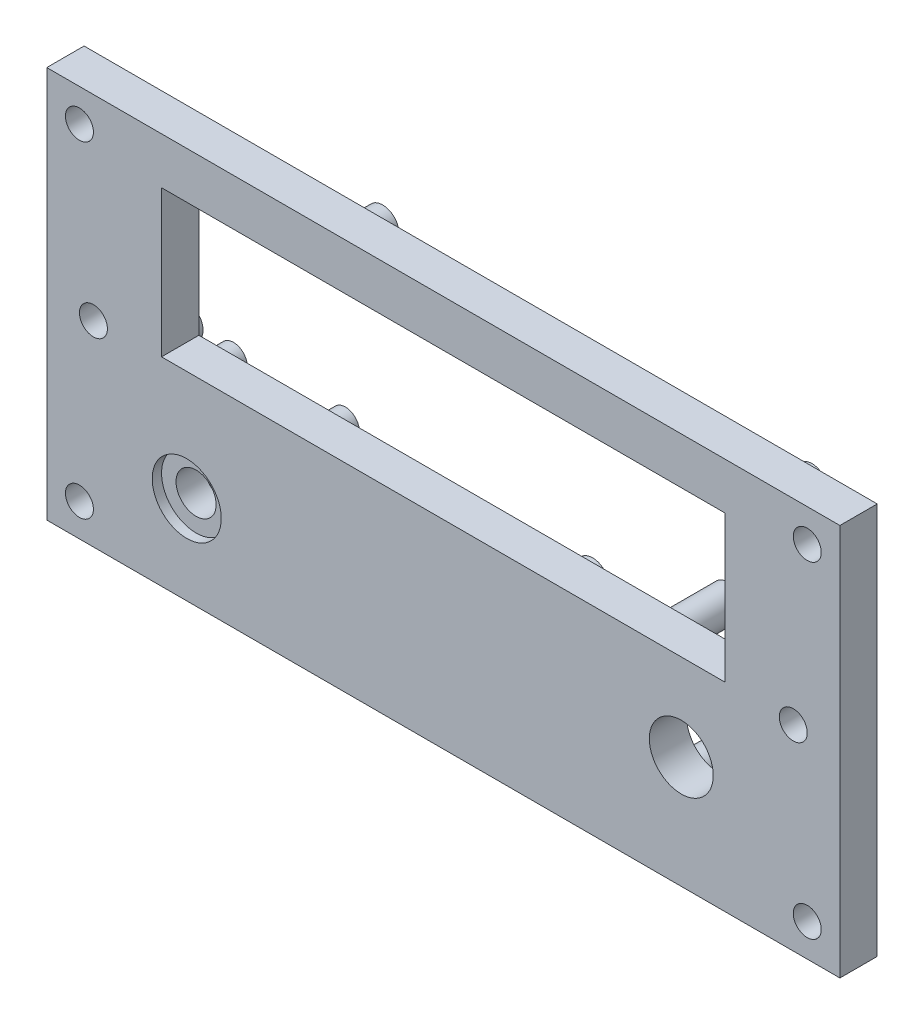
SolidWorks part; units mm, degrees
ref_plane "Front Plane" through (0, 0, 0) normal (0, 0, 1) x (1, 0, 0)
ref_plane "Top Plane" through (0, 0, 0) normal (0, 1, 0) x (1, 0, 0)
ref_plane "Right Plane" through (0, 0, 0) normal (1, 0, 0) x (0, 0, -1)
sketch "Sketch1" plane through (0, 0, 0) normal (0, 0, 1) x (1, 0, 0)
  line L1 (-42.5, 21) -> (42.5, 21)
  line L2 (-42.5, 21) -> (-42.5, -21)
  line L3 (-42.5, -21) -> (42.5, -21)
  line L4 (42.5, 21) -> (42.5, -21)
  dimension "D1" = 42
  dimension "D2" = 85
  dimension "D3" = 42.5
  dimension "D4" = 21
extrude "Bottom Plate" add sketch "Sketch1" along normal blind 4
sketch "Sketch2" plane through (0, 0, 4) normal (0, 0, 1) x (1, 0, 0)
  line L0 (-42.5, 21) -> (-42.5, -21) construction
  line L1 (42.5, 21) -> (-42.5, 21) construction
  line L2 (-52.893, 0) -> (50.3608, 0) construction
  line L3 (0, 34.5809) -> (0, -29.7625) construction
  circle A0 centre (-39, 17.5) radius 1.5
  circle A1 centre (-39, -17.5) radius 1.5
  circle A2 centre (39, -17.5) radius 1.5
  circle A3 centre (39, 17.5) radius 1.5
  dimension "D1" = 3
  dimension "D2" = 3.5
  dimension "D3" = 3.5
extrude "Bottom Plate Screw Holes" cut sketch "Sketch2" against normal through all both and the other way through all
sketch "Sketch15" plane through (0, 0, 4) normal (0, 0, 1) x (1, 0, 0)
  line L0 (0, 37.6052) -> (0, -29.8282) construction
  line L1 (-42.5, 21) -> (-42.5, -21) construction
  line L2 (-42.5, -21) -> (42.5, -21) construction
  circle A0 centre (-37.5, 0) radius 1.5
  circle A1 centre (37.5, 0) radius 1.5
  dimension "D1" = 3
  dimension "D2" = 5
  dimension "D3" = 21
  dimension "D4" = 0
extrude "Top Plate Screws Holes" cut sketch "Sketch15" against normal blind 2.5 and the other way through all
sketch "Sketch5" plane through (0, 0, 4) normal (0, 0, 1) x (1, 0, 0)
  line L1 (-30.2, 16) -> (30.2, 16)
  line L2 (-30.2, 16) -> (-30.2, 0.3)
  line L3 (-30.2, 0.3) -> (30.2, 0.3)
  line L4 (30.2, 16) -> (30.2, 0.3)
  line L5 (42.5, 21) -> (-42.5, 21) construction
  line L6 (-42.5, 21) -> (-42.5, -21) construction
  dimension "D1" = 60.4
  dimension "D2" = 15.7
  dimension "D3" = 12.3
  dimension "D4" = 5
extrude "LED" cut sketch "Sketch5" against normal through all both and the other way through all
sketch "Sketch16" plane through (0, 0, 0) normal (0, 0, -1) x (-1, 0, 0)
  line L0 (42.5, 21) -> (42.5, -21) construction
  line L1 (-42.5, 21) -> (42.5, 21) construction
  line L2 (-42.5, -21) -> (-42.5, 21) construction
  line L3 (42.5, -21) -> (-42.5, -21) construction
  circle A0 centre (-33.5, 17.5) radius 1.75
  circle A1 centre (-10, -3) radius 1.75
  circle A2 centre (33.5, -1) radius 1.75
  circle A3 centre (12.5, 18.5) radius 1.75
  circle A4 centre (13.75, -16.5) radius 1.75
  dimension "D1" = 3.5
  dimension "D2" = 3.5
  dimension "D3" = 3.5
  dimension "D4" = 3.5
  dimension "D13" = 3.5
  dimension "D5" = 9
  dimension "D6" = 22
  dimension "D7" = 30
  dimension "D8" = 2.5
  dimension "D9" = 9
  dimension "D10" = 3.5
  dimension "D11" = 32.5
  dimension "D12" = 18
  dimension "D14" = 4.5
  dimension "D15" = 28.75
extrude "LED Board Support" add sketch "Sketch16" along normal blind 2
sketch "Sketch17" plane through (0, 0, -2) normal (0, 0, -1) x (-1, 0, 0)
  circle A0 centre (-33.5, 17.5) radius 1
  circle A1 centre (-10, -3) radius 1
  circle A2 centre (12.5, 18.5) radius 1
  circle A3 centre (33.5, -1) radius 1
  circle A4 centre (13.75, -16.5) radius 1
  dimension "D1" = 2
  dimension "D2" = 2
  dimension "D3" = 2
  dimension "D4" = 2
  dimension "D5" = 2
extrude "Led Board Screws Holes" cut sketch "Sketch17" against normal blind 5
sketch "Sketch6" plane through (0, 0, 4) normal (0, 0, 1) x (1, 0, 0)
  line L0 (-42.5, 21) -> (-42.5, -21) construction
  line L1 (-42.5, -21) -> (42.5, -21) construction
  circle A0 centre (-27.5, -11.5) radius 2.15
  dimension "D1" = 4.3
  dimension "D2" = 15
  dimension "D3" = 9.5
extrude "TestButton Cut" cut sketch "Sketch6" against normal through all both
sketch "Sketch10" plane through (0, 0, 4) normal (0, 0, 1) x (1, 0, 0)
  circle A0 centre (-27.5, -11.5) radius 3.7
  dimension "D1" = 7.4
extrude "TestButton Big Cut" cut sketch "Sketch10" against normal blind 1
sketch "Sketch13" plane through (0, 0, 0) normal (0, 0, -1) x (-1, 0, 0)
  line L0 (42.5, 21) -> (42.5, -21) construction
  line L1 (42.5, -21) -> (-42.5, -21) construction
  line L2 (19.2797, -11.5) -> (38.8917, -11.5) construction
  circle A0 centre (21.5, -7) radius 1.5
  circle A1 centre (33.5, -7) radius 1.5
  circle A2 centre (33.5, -16) radius 1.5
  circle A3 centre (21.5, -16) radius 1.5
  dimension "D1" = 3
  dimension "D2" = 3
  dimension "D3" = 9
  dimension "D4" = 12
  dimension "D5" = 14
  dimension "D6" = 0
  dimension "D7" = 9.5
extrude "Test Board Support" add sketch "Sketch13" along normal blind 7
sketch "Sketch14" plane through (0, 0, -7) normal (0, 0, -1) x (-1, 0, 0)
  circle A0 centre (21.5, -16) radius 1
  circle A1 centre (21.5, -7) radius 1
  circle A2 centre (33.5, -7) radius 1
  circle A3 centre (33.5, -16) radius 1
  dimension "D1" = 2
  dimension "D2" = 2
  dimension "D3" = 2
  dimension "D4" = 2
extrude "Test Board Screws Hole" cut sketch "Sketch14" against normal blind 5
sketch "Sketch9" plane through (0, 0, 0) normal (0, 0, -1) x (-1, 0, 0)
  line L0 (-42.5, -21) -> (-42.5, 21) construction
  line L1 (42.5, -21) -> (-42.5, -21) construction
  circle A0 centre (-25.5, -9) radius 3.425
  dimension "D2" = 6.85
  dimension "D1" = 17
  dimension "D3" = 12
extrude "Brt Add" cut sketch "Sketch9" against normal blind 6
sketch "Sketch11" plane through (0, 0, 0) normal (0, 0, -1) x (-1, 0, 0)
  line L0 (-42.5, -21) -> (-42.5, 21) construction
  line L1 (42.5, -21) -> (-42.5, -21) construction
  line L2 (-36.5852, -11) -> (-13.9594, -11) construction
  circle A0 centre (-32.5, -4) radius 1.75
  circle A1 centre (-18.5, -4) radius 1.75
  circle A2 centre (-18.5, -18) radius 1.75
  circle A3 centre (-32.5, -18) radius 1.75
  dimension "D1" = 3.5
  dimension "D2" = 3.5
  dimension "D3" = 0
  dimension "D4" = 10
  dimension "D5" = 17
  dimension "D6" = 14
  dimension "D7" = 10
extrude "Pot Board Support" add sketch "Sketch11" along normal blind 8
sketch "Sketch12" plane through (0, 0, -8) normal (0, 0, -1) x (-1, 0, 0)
  circle A0 centre (-32.5, -4) radius 1
  circle A1 centre (-18.5, -4) radius 1
  circle A2 centre (-18.5, -18) radius 1
  circle A3 centre (-32.5, -18) radius 1
  dimension "D1" = 2
  dimension "D2" = 2
  dimension "D3" = 2
  dimension "D4" = 2
  dimension "D5" = 14
  dimension "D6" = 14
extrude "Pot Board Screws Hole" cut sketch "Sketch12" against normal blind 5
